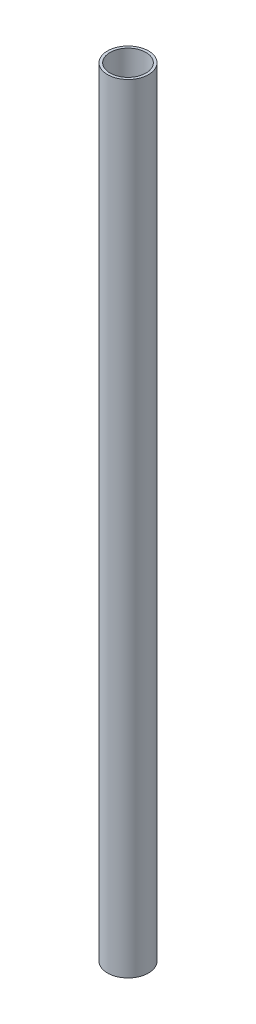
SolidWorks part; units mm, degrees
material "Plain Carbon Steel"
ref_plane "Front Plane" through (0, 0, 0) normal (0, 0, 1) x (1, 0, 0)
ref_plane "Top Plane" through (0, 0, 0) normal (0, 1, 0) x (1, 0, 0)
ref_plane "Right Plane" through (0, 0, 0) normal (1, 0, 0) x (0, 0, -1)
sketch "Sketch1" plane through (0, 0, 0) normal (0, -1, 0) x (1, 0, 0)
  circle A2 centre (0, 0) radius 8.325
  circle A3 centre (0, 0) radius 9.525
  dimension "D1" = 19.05
  dimension "D2" = 1.2
extrude "Extrude1" add sketch "Sketch1" along normal blind 361
sketch3d "3DSketch1"
  line L0 (0, -40.1072, 0) -> (0, -420.9896, 0) construction
  line L1 (0, -361, 0) -> (0, 0, 0) construction
  line L2 (0, -361, 0) -> (0, 0, 0) construction
